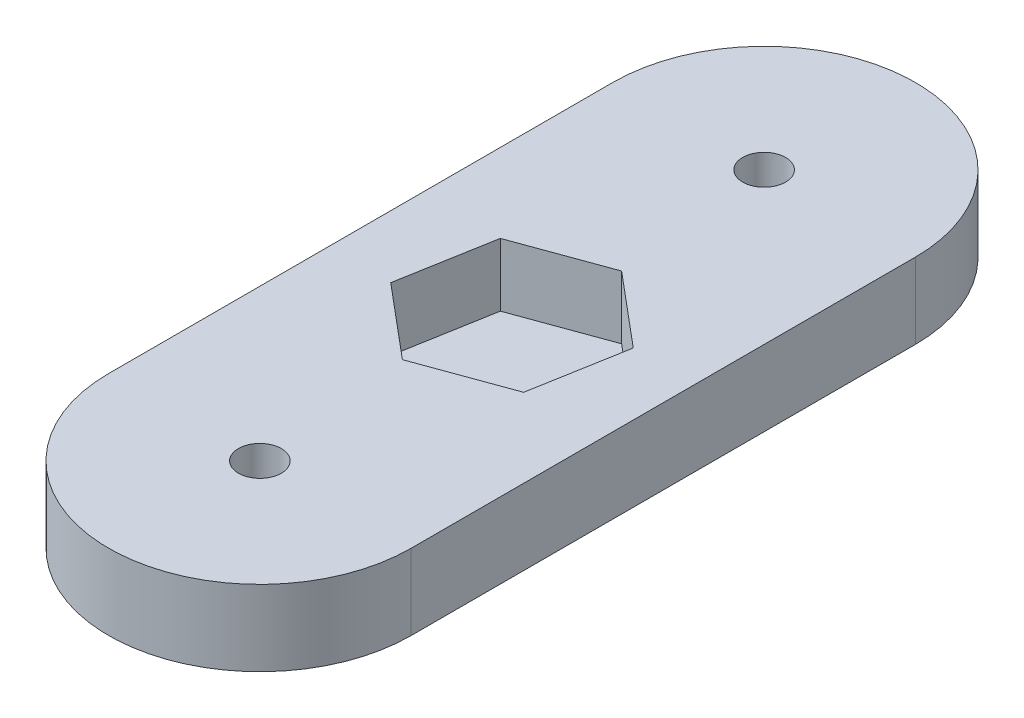
SolidWorks part; units mm, degrees
material "ABS PC"
ref_plane "Front Plane" through (0, 0, 0) normal (0, 0, 1) x (1, 0, 0)
ref_plane "Top Plane" through (0, 0, 0) normal (0, 1, 0) x (1, 0, 0)
ref_plane "Right Plane" through (0, 0, 0) normal (1, 0, 0) x (0, 0, -1)
sketch "Sketch1" plane through (0, 0, 0) normal (0, 1, 0) x (1, 0, 0)
  line L0 (0, 0) -> (0, 40) construction
  line L1 (-12, 0) -> (-12, 40)
  line L2 (12, 0) -> (12, 40)
  arc A0 (-12, 0) -> (12, 0) centre (0, 0) ccw
  arc A1 (12, 40) -> (-12, 40) centre (0, 40) ccw
  circle A2 centre (0, 40) radius 1.7
  circle A3 centre (0, 0) radius 1.7
  point P3 (0, 20)
  dimension "D2" = 40
  dimension "D3" = 3.4
  dimension "D1" = 24
extrude "Boss-Extrude1" add sketch "Sketch1" along normal blind 6
sketch "Sketch2" plane through (0, 6, 0) normal (0, 1, 0) x (1, 0, 0)
  line L0 (12, 0) -> (12, 40) construction
  line L1 (5.7496, 15.1755) -> (7.0529, 22.5671)
  line L2 (7.0529, 22.5671) -> (1.3033, 27.3915)
  line L3 (1.3033, 27.3915) -> (-5.7496, 24.8245)
  line L4 (-5.7496, 24.8245) -> (-7.0529, 17.4329)
  line L5 (-7.0529, 17.4329) -> (-1.3033, 12.6085)
  line L6 (-1.3033, 12.6085) -> (5.7496, 15.1755)
  line L7 (-12, 40) -> (-12, 0) construction
  circle A0 centre (0, 20) radius 6.5 construction
  dimension "D1" = 13
  dimension "D2" = 12
  dimension "D3" = 20
  dimension "D4" = 110
extrude "Cut-Extrude1" cut sketch "Sketch2" against normal blind 5
